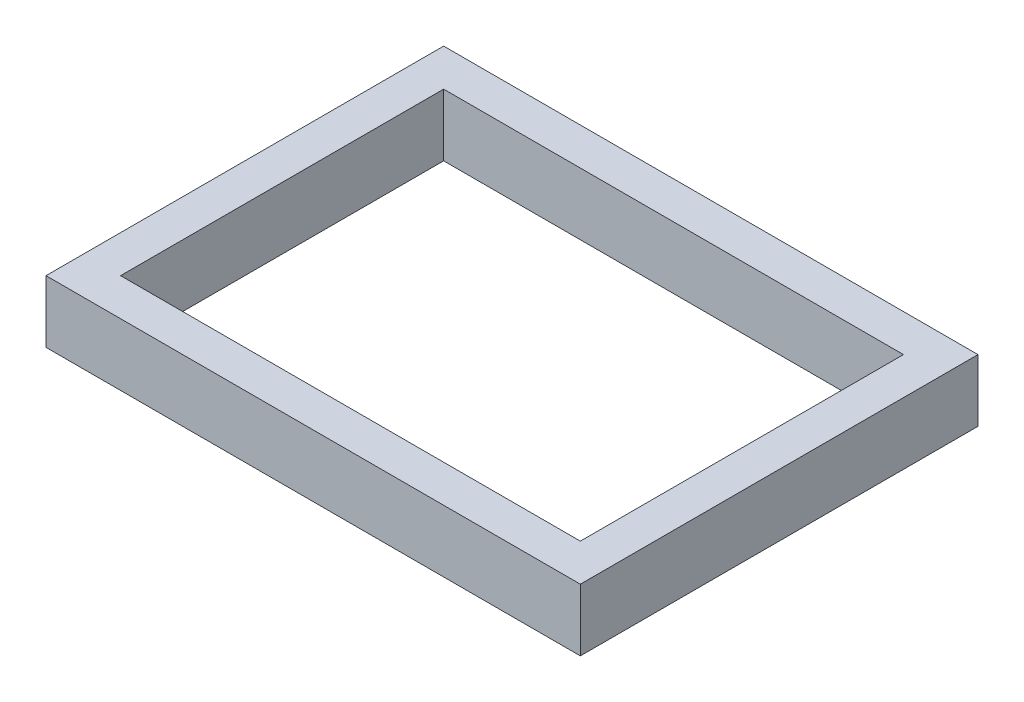
SolidWorks part; units mm, degrees
ref_plane "Front Plane" through (0, 0, 0) normal (0, 0, 1) x (1, 0, 0)
ref_plane "Top Plane" through (0, 0, 0) normal (0, 1, 0) x (1, 0, 0)
ref_plane "Right Plane" through (0, 0, 0) normal (1, 0, 0) x (0, 0, -1)
sketch "Sketch1" plane through (0, 0, 0) normal (0, 1, 0) x (1, 0, 0)
  line L1 (0, 0) -> (37, 0)
  line L2 (0, 0) -> (0, 26)
  line L3 (0, 26) -> (37, 26)
  line L4 (37, 0) -> (37, 26)
  line L5 (-3, -3) -> (40, -3)
  line L6 (-3, -3) -> (-3, 29)
  line L7 (-3, 29) -> (40, 29)
  line L8 (40, -3) -> (40, 29)
  dimension "D1" = 26
  dimension "D2" = 37
  dimension "D3" = 3
  dimension "D4" = 3
  dimension "D5" = 3
  dimension "D6" = 3
extrude "Boss-Extrude1" add sketch "Sketch1" along normal blind 5
